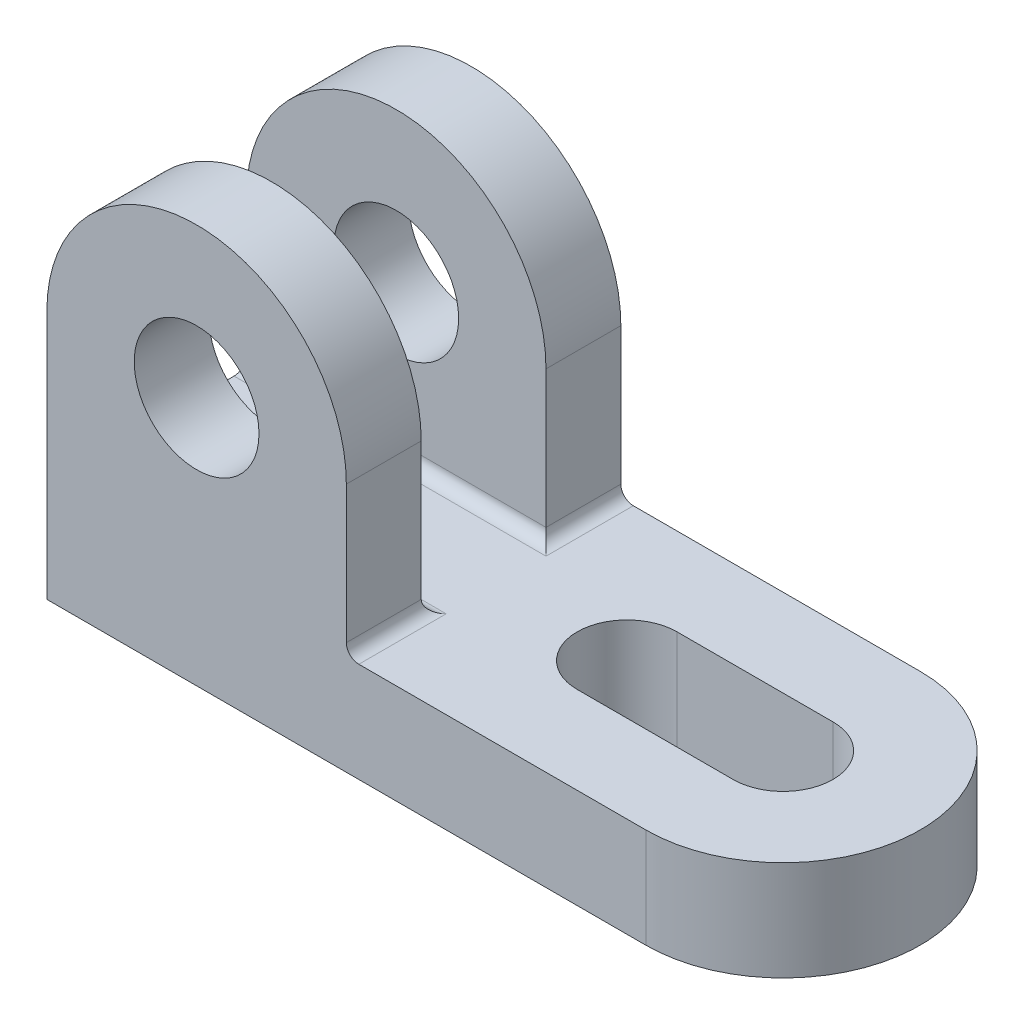
SolidWorks part; units mm, degrees
ref_plane "Front Plane" through (0, 0, 0) normal (0, 0, 1) x (1, 0, 0)
ref_plane "Top Plane" through (0, 0, 0) normal (0, 1, 0) x (1, 0, 0)
ref_plane "Right Plane" through (0, 0, 0) normal (1, 0, 0) x (0, 0, -1)
sketch "Sketch2" plane through (0, 0, 0) normal (0, 1, 0) x (1, 0, 0)
  line L1 (-59, 22) -> (59, 22)
  line L2 (-59, 22) -> (-59, -22)
  line L3 (-59, -22) -> (59, -22)
  line L4 (59, 22) -> (59, -22)
  line L5 (-59, 22) -> (59, -22) construction
  line L6 (-59, -22) -> (59, 22) construction
  circle A0 centre (37, 0) radius 22
  point P0 (0, 0)
  dimension "D1" = 118
  dimension "D2" = 44
extrude "Boss-Extrude1" add sketch "Sketch2" along normal blind 16 contours A0 L1 L2 L3 | A0
sketch "Sketch5" plane through (0, 16, 0) normal (0, 1, 0) x (1, 0, 0)
  line L0 (37, 0) -> (12, 0) construction
  line L1 (37, -8) -> (12, -8)
  line L2 (37, 8) -> (12, 8)
  arc A0 (37, -8) -> (37, 8) centre (37, 0) ccw
  arc A1 (12, 8) -> (12, -8) centre (12, 0) ccw
  point P4 (24.5, 0)
  dimension "D2" = 8
  dimension "D1" = 25
extrude "Cut-Extrude1" cut sketch "Sketch5" against normal through all
sketch "Sketch6" plane through (0, 0, 22) normal (0, 0, 1) x (1, 0, 0)
  line L0 (-59, 0) -> (37, 0) construction
  line L1 (-59, 16) -> (-11, 16)
  line L2 (-59, 16) -> (-59, 40)
  line L3 (-59, 40) -> (-11, 40)
  line L4 (-11, 16) -> (-11, 40)
  circle A0 centre (-35, 40) radius 24
  circle A1 centre (-35, 40) radius 10
  line M5 (37, 16) -> (-59, 16)
  dimension "D3" = 20
  dimension "D1" = 40
  dimension "D2" = 48
extrude "Boss-Extrude2" add sketch "Sketch6" against normal blind 12 contours A1 L3 A0 | A1 L3 A0 | A0 L4 M5 | A0 L2 L1
mirror "Mirror1" about plane through (0, 0, 0) normal (0, 0, 1) of "Boss-Extrude2"
fillet "Fillet1" radius 2 4 edges at (-35, 16, -10) (-11, 16, -16) (-35, 16, 10) (-11, 16, 16)
